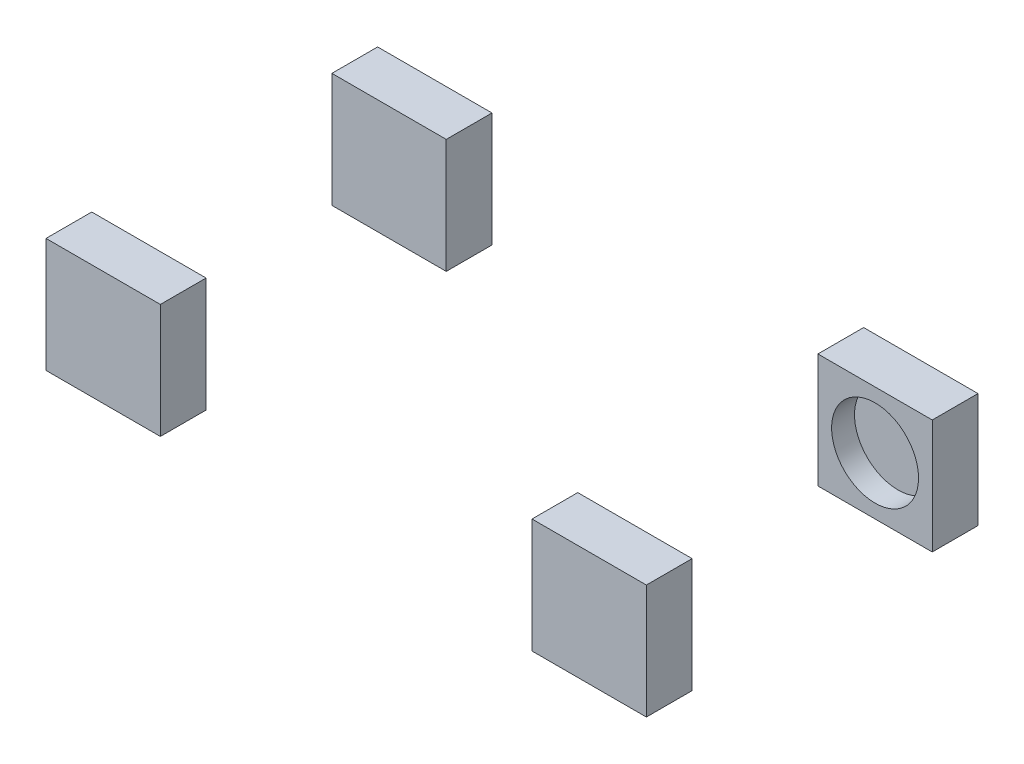
SolidWorks part; units mm, degrees
ref_plane "Front Plane" through (0, 0, 0) normal (0, 0, 1) x (1, 0, 0)
ref_plane "Top Plane" through (0, 0, 0) normal (0, 1, 0) x (1, 0, 0)
ref_plane "Right Plane" through (0, 0, 0) normal (1, 0, 0) x (0, 0, -1)
sketch "Sketch1" plane through (0, 0, 0) normal (0, 1, 0) x (1, 0, 0)
  line L0 (0, 175.6005) -> (0, -163.1385) construction
  line L1 (-212.5, -125) -> (212.5, -125)
  line L2 (-212.5, -125) -> (-212.5, 125)
  line L3 (-212.5, 125) -> (212.5, 125)
  line L4 (212.5, -125) -> (212.5, 125)
  line L5 (-212.5, -125) -> (212.5, 125) construction
  line L6 (-212.5, 125) -> (212.5, -125) construction
  line L7 (162.5, 105) -> (262.5, 105)
  line L8 (162.5, 105) -> (162.5, 145)
  line L9 (162.5, 145) -> (262.5, 145)
  line L10 (262.5, 105) -> (262.5, 145)
  line L11 (162.5, 105) -> (262.5, 145) construction
  line L12 (162.5, 145) -> (262.5, 105) construction
  line L13 (162.5, -105) -> (262.5, -105)
  line L14 (162.5, -105) -> (162.5, -145)
  line L15 (162.5, -145) -> (262.5, -145)
  line L16 (262.5, -105) -> (262.5, -145)
  line L17 (162.5, -105) -> (262.5, -145) construction
  line L18 (162.5, -145) -> (262.5, -105) construction
  line L19 (-231.0788, 0) -> (285.5483, 0) construction
  line L20 (-162.5, -145) -> (-262.5, -145)
  line L21 (-262.5, -105) -> (-262.5, -145)
  line L22 (-162.5, -105) -> (-262.5, -105)
  line L23 (-162.5, -105) -> (-162.5, -145)
  line L24 (-162.5, 145) -> (-262.5, 145)
  line L25 (-262.5, 105) -> (-262.5, 145)
  line L26 (-162.5, 105) -> (-262.5, 105)
  line L27 (-162.5, 105) -> (-162.5, 145)
  point P0 (0, 0)
  dimension "D1" = 425
  dimension "D2" = 250
  dimension "D3" = 100
  dimension "D4" = 40
  dimension "D5" = 40
  dimension "D6" = 100
extrude "Boss-Extrude1" add sketch "Sketch1" along normal mid plane 100 contours L3 L27 L24 L25 L26 L2 | L26 L27 L3 L2 | L7 L10 L9 L8 L3 L4 | L8 L7 L4 L3 | L16 L13 L4 L1 L14 L15 | L23 L1 L2 L22 L21 L20 | L23 L22 L2 L1
sketch "Sketch3" plane through (0, 0, 105) normal (0, 0, -1) x (-1, 0, 0)
  line L0 (-212.5, 50) -> (-212.5, -50) construction
  line L1 (-162.5, 50) -> (-262.5, 50) construction
  line L2 (-162.5, -50) -> (-262.5, -50) construction
  line L3 (-262.5, 0) -> (-162.5, 0) construction
  line L4 (-262.5, 50) -> (-262.5, -50) construction
  line L5 (-162.5, 50) -> (-162.5, -50) construction
  circle A0 centre (-212.5, 0) radius 38
  dimension "D1" = 76
extrude "Cut-Extrude5" cut sketch "Sketch3" against normal blind 20
sketch "Sketch4" plane through (0, 0, -105) normal (0, 0, 1) x (1, 0, 0)
  circle A0 centre (212.5, 0) radius 38 construction
  circle A1 centre (212.5, 0) radius 38
extrude "Cut-Extrude6" cut sketch "Sketch4" against normal blind 20
sketch3d "3DSketch4" plane through (0, 0, 0) normal (0, 0, 1) x (1, 0, 0)
  dimension "D1" = 8.42
sketch "Mech Trail & Caster" plane through (0, 0, 116.58) normal (0, 0, -1) x (-1, 0, 0)
  line L0 (-212.5, 38) -> (-212.5, -50) construction
  line L1 (-250.5, 0) -> (-174.5, 0) construction
  line L2 (-162.5, -50) -> (-262.5, -50) construction
  line L3 (-162.5, -50) -> (-262.5, -50)
  line L4 (-208.5, -50) -> (-212.5, -27) construction
  line L5 (-212.5, -27) -> (-225.6719, 48.7387) construction
  line L6 (-162.5, 50) -> (-262.5, 50) construction
  line L7 (-162.5, 50) -> (-262.5, 50)
  circle A0 centre (-212.5, 0) radius 38 construction
  circle A1 centre (-212.5, 0) radius 38
  point P7 (-212.5, -27)
  point P15 (-221.8913, 27)
  dimension "D1" = 23
  dimension "D2" = 4
  dimension "D3" = 23
  dimension "D4" = 9.866
sketch3d "3DSketch5"
  line L0 (212.5, 38, 116.58) -> (212.5, -50, 116.58) construction
  line L1 (250.5, 0, 116.58) -> (174.5, 0, 116.58) construction
sketch "Sketch6" plane through (221.8913, 0, 0) normal (1, 0, 0) x (0, 0, -1)
  line L0 (-116.58, 27) -> (-110.904, 27) construction
  point P0 (-116.58, 27)
  point P5 (-110.904, 27)
  dimension "D1" = 5.676
sketch3d "KPI angle/ steering axis"
  line L0 (221.8913, 27, 110.904) -> (212.5, -27, 116.58) construction
  point P0 (221.8913, 27, 110.904)
  point P2 (212.5, -27, 116.58)
sketch3d "3DSketch8" plane through (0, 0, 0) normal (0, 0, 1) x (1, 0, 0)
  dimension "D1" = 8.42
sketch "Sketch7" plane through (0, 0, -116.58) normal (0, 0, 1) x (1, 0, 0)
  line L0 (212.5, 50) -> (212.5, -50) construction
  line L1 (162.5, 50) -> (262.5, 50) construction
  line L2 (162.5, -50) -> (262.5, -50) construction
  line L3 (162.5, 0) -> (262.5, 0) construction
  line L4 (162.5, 50) -> (162.5, -50) construction
  line L5 (262.5, 50) -> (262.5, -50) construction
  line L6 (221.8913, 27) -> (212.5, -27) construction
  line L7 (221.8913, 27) -> (212.5, -27) construction
  point P12 (212.5, -27)
  point P13 (221.8913, 27)
sketch3d "3DSketch9"
  line L0 (212.5, 50, -116.58) -> (212.5, -50, -116.58) construction
  line L1 (162.5, 0, -116.58) -> (262.5, 0, -116.58) construction
sketch "Sketch8" plane through (221.8913, 0, 0) normal (-1, 0, 0) x (0, 0, 1)
  line L0 (-116.58, 27) -> (-110.91, 27) construction
  point P0 (-116.58, 27)
  point P5 (-110.91, 27)
  dimension "D1" = 5.67
sketch3d "3DSketch10"
  line L0 (221.8913, 27, -110.91) -> (212.5, -27, -116.58) construction
sketch3d "3DSketch11"
  line L0 (221.8913, 27, -116.58) -> (221.8913, 27, -110.91) construction
  line L1 (212.5, 50, -105) -> (212.5, -50, -105) construction
  line L2 (162.5, 50, -105) -> (262.5, 50, -105) construction
  line L3 (162.5, -50, -105) -> (262.5, -50, -105) construction
sketch "Front view IC's/RC" plane through (212.5, 0, 0) normal (-1, 0, 0) x (0, 0, 1)
  line L0 (-110.91, 27) -> (-89.7206, 27) construction
  line L1 (-110.91, 27) -> (285.7, -26.9974) construction
  line L2 (110.904, 27) -> (85.1327, 27) construction
  line L3 (110.904, 27) -> (-285.706, -26.9974) construction
  line L4 (-125, 50) -> (-125, -50) construction
  line L5 (-105, 50) -> (-145, 50) construction
  line L6 (-105, -50) -> (-145, -50) construction
  line L7 (125, 50) -> (125, -50) construction
  line L8 (105, 50) -> (145, 50) construction
  line L9 (105, -50) -> (145, -50) construction
  line L10 (-285.706, -26.9974) -> (285.7, -26.9974) construction
  line L11 (-125, -50) -> (285.7, -26.9974) construction
  line L12 (-285.706, -26.9974) -> (125, -50) construction
  line L13 (0, 78.2039) -> (0, -138.8888) construction
  point P20 (-116.58, -27)
  point P21 (116.58, -27)
  point P29 (0, -42.999)
  dimension "D1" = 7.753
  dimension "D2" = 396.61
  dimension "D3" = 7.753
  dimension "D4" = 396.61
  dimension "D5" = 7.001
  dimension "D6" = 410.706
sketch3d "3DSketch12" plane through (0, 0, 0) normal (0, 0, 1) x (1, 0, 0)
  dimension "D1" = 20
sketch "Left side IC's/PC" plane through (0, 0, -125) normal (0, 0, -1) x (-1, 0, 0)
  line L0 (162.5, -50) -> (262.5, -50) construction
  line L1 (162.5, 50) -> (262.5, 50) construction
  line L2 (162.5, -50) -> (262.5, -50)
  line L3 (162.5, 50) -> (262.5, 50)
  line L4 (212.5, 50) -> (212.5, -50) construction
  line L5 (162.5, 0) -> (262.5, 0) construction
  line L6 (162.5, 50) -> (162.5, -50) construction
  line L7 (262.5, 50) -> (262.5, -50) construction
  line L8 (-212.5, 50) -> (-212.5, -50) construction
  line L9 (-212.5, 50) -> (-212.5, -50) construction
  line L10 (-393.1005, -27) -> (329.5904, -27) construction
  line L11 (-221.8913, 27) -> (400.1441, -57.6885) construction
  line L12 (-221.8913, 27) -> (-156.9239, 27) construction
  line L13 (212.5, 27) -> (-336.1216, -104.3782) construction
  line L14 (212.5, 27) -> (147.1014, 27) construction
  line L15 (-212.5, -50) -> (174.7378, -27) construction
  line L16 (-12.9983, -27) -> (212.5, -50) construction
  point P12 (212.5, 27)
  point P13 (212.5, -27)
  point P14 (-212.5, -27)
  point P18 (56.0921, -34.047)
  point P27 (-12.9983, -27)
  point P29 (174.7378, -27)
  point P33 (-221.8913, 27)
  dimension "D1" = 23
  dimension "D2" = 54
  dimension "D3" = 7.753
  dimension "D4" = 13.467
  dimension "D5" = 225.4983
  dimension "D6" = 387.2378
  dimension "D7" = 15.953
  dimension "D8" = 268.5921
sketch3d "3DSketch13" plane through (0, 0, 0) normal (0, 0, 1) x (1, 0, 0)
  dimension "D1" = 20
sketch "Right side IC's/PC" plane through (0, 0, 125) normal (0, 0, -1) x (-1, 0, 0)
  line L0 (212.5, 50) -> (212.5, -50) construction
  line L1 (-221.8913, 27) -> (309.2663, -45.3157) construction
  line L2 (-221.8913, 27) -> (-150.1998, 27) construction
  line L3 (212.5, 27) -> (-290.0341, -93.3417) construction
  line L4 (162.5, -50) -> (262.5, -50)
  line L5 (262.5, -50) -> (262.5, 50)
  line L6 (262.5, 50) -> (162.5, 50)
  line L7 (162.5, 50) -> (162.5, -50)
  line L8 (162.5, -50) -> (262.5, -50)
  line L9 (262.5, -50) -> (262.5, 50)
  line L10 (262.5, 50) -> (162.5, 50)
  line L11 (162.5, 50) -> (162.5, -50)
  line L12 (212.5, 27) -> (139.4199, 27) construction
  line L13 (-212.5, -27) -> (212.5, -27) construction
  line L20 (-212.5, 50) -> (-212.5, -50) construction
  line L21 (-212.5, -50) -> (174.7378, -27) construction
  line L22 (212.5, -50) -> (-12.9983, -27) construction
  point P6 (212.5, -27)
  point P7 (212.5, 27)
  point P8 (-221.8913, 27)
  point P10 (174.7378, -27)
  point P24 (56.0921, -34.047)
  point P29 (-12.9983, -27)
  dimension "D2" = 23
  dimension "D3" = 54
  dimension "D4" = 7.753
  dimension "D5" = 13.467
  dimension "D6" = 225.4983
  dimension "D7" = 387.2378
  dimension "D8" = 15.953
  dimension "D1" = 0
sketch3d "3DSketch14" plane through (0, 0, 0) normal (0, 0, 1) x (1, 0, 0)
  dimension "D1" = 50
sketch "Rear view IC's/RC" plane through (-212.5, 0, 0) normal (1, 0, 0) x (0, 0, -1)
  line L0 (-125, 50) -> (-125, -50) construction
  line L1 (-105, 50) -> (-145, 50) construction
  line L2 (-105, -50) -> (-145, -50) construction
  line L3 (125, 50) -> (125, -50) construction
  line L4 (105, 50) -> (145, 50) construction
  line L5 (105, -50) -> (145, -50) construction
  line L6 (0, 69.5621) -> (0, -61.9838) construction
  line L7 (-193.1722, -27) -> (206.3811, -27) construction
  line L8 (-110.91, 27) -> (114.5883, -27) construction
  line L9 (-110.91, 27) -> (-74.4999, 27) construction
  line L10 (110.91, 27) -> (79.0484, 27) construction
  line L11 (110.91, 27) -> (-114.5883, -27) construction
  line L12 (-125, -50) -> (114.5883, -27) construction
  line L13 (-114.5883, -27) -> (125, -50) construction
  point P12 (-110.91, 27)
  point P13 (-110.91, -27)
  point P17 (110.91, -27)
  point P18 (110.91, 27)
  point P26 (0, -38.0002)
  point P28 (114.5883, -27)
  point P30 (-114.5883, -27)
  dimension "D1" = 23
  dimension "D2" = 14.09
  dimension "D3" = 54
  dimension "D4" = 13.467
  dimension "D5" = 13.467
  dimension "D6" = 239.5883
  dimension "D7" = 11.9998
sketch3d "Chassis hardpoint plane LF upper "
  line L0 (-174.7378, -27, -125) -> (212.5, -26.9974, 285.7) construction
  point P0 (212.5, -26.9974, 285.7)
  point P2 (-174.7378, -27, -125)
  point P6 (221.8913, 27, -110.91)
sketch3d "Chassis hardpoint plane RF upper"
  line L0 (-174.7378, -27, 125) -> (212.5, -26.9974, -285.706) construction
  point P0 (221.8913, 27, 110.904)
  point P2 (212.5, -26.9974, -285.706)
  point P4 (-174.7378, -27, 125)
sketch3d "Chassis hardpoint plane RF/LF & LR/RR lower"
  line L0 (-174.7378, -27, 125) -> (212.5, -26.9974, -285.706) construction
  point P0 (212.5, -27, 116.58)
  point P2 (212.5, -26.9974, -285.706)
  point P4 (-174.7378, -27, 125)
sketch3d "Chassis hardpoint plane RR upper"
  line L0 (-212.5, -27, -114.5883) -> (12.9983, -27, 125) construction
  point P0 (-212.5, 27, 110.91)
  point P2 (12.9983, -27, 125)
  point P4 (-212.5, -27, -114.5883)
sketch3d "Chassis hardpoint plane LR upper"
  line L0 (-212.5, -27, 114.5883) -> (12.9983, -27, -125) construction
  point P0 (-212.5, -27, 114.5883)
  point P2 (-212.5, 27, -110.91)
  point P5 (12.9983, -27, -125)
